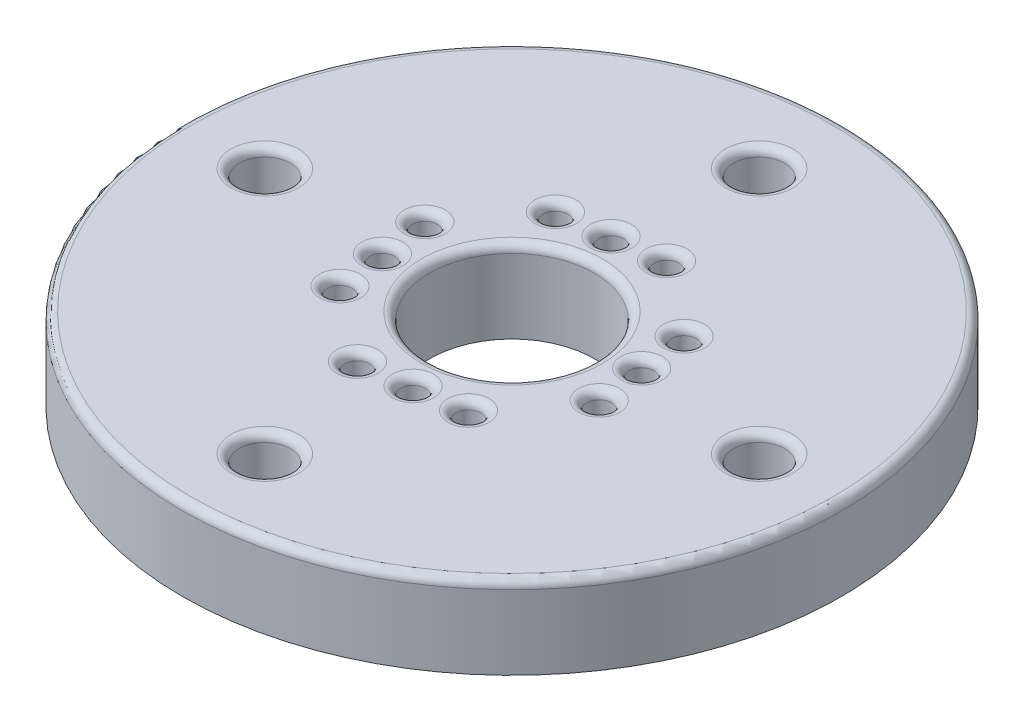
SolidWorks part; units mm, degrees
ref_plane "Piano frontale" through (0, 0, 0) normal (0, 0, 1) x (1, 0, 0)
ref_plane "Piano superiore" through (0, 0, 0) normal (0, 1, 0) x (1, 0, 0)
ref_plane "Piano destro" through (0, 0, 0) normal (1, 0, 0) x (0, 0, -1)
sketch "Schizzo1" plane through (0, 0, 0) normal (0, 1, 0) x (1, 0, 0)
  line L0 (0, 18.2203) -> (0, -20.6735) construction
  line L1 (-18.4196, 0) -> (19.4331, 0) construction
  circle A0 centre (0, 0) radius 15 construction
  circle A2 centre (0, 15) radius 1.55
  circle A3 centre (15, 0) radius 1.55
  circle A4 centre (0, -15) radius 1.55
  circle A5 centre (-15, 0) radius 1.55
  circle A6 centre (0, 0) radius 5
  circle A7 centre (0, 0) radius 20
  dimension "D1" = 30
  dimension "D2" = 3.1
  dimension "D3" = 10
  dimension "D4" = 40
extrude "Estrusione-Estrusione1" add sketch "Schizzo1" along normal blind 5
fillet "Raccordo1" radius 0.5 6 edges at (0, 5, 5) (0, 5, 16.55) (0, 5, -13.45) (0, 5, 20) (15, 5, 1.55) (-15, 5, 1.55)
sketch "Schizzo2" plane through (0, 0, 0) normal (0, -1, 0) x (1, 0, 0)
  circle A0 centre (0, 0) radius 10.35 construction
  circle A1 centre (0, 0) radius 20
  circle A2 centre (0, 0) radius 20
  circle A3 centre (-7.3362, -2.0447) radius 0.75 construction
  circle A4 centre (-6.9381, 0.9288) radius 0.75 construction
  circle A5 centre (-6.5401, 3.9023) radius 0.75 construction
  circle A6 centre (-2.0447, 7.3362) radius 0.75 construction
  circle A7 centre (0.9288, 6.9381) radius 0.75 construction
  circle A8 centre (3.9023, 6.5401) radius 0.75 construction
  circle A9 centre (7.3362, 2.0447) radius 0.75 construction
  circle A10 centre (6.9381, -0.9288) radius 0.75 construction
  circle A11 centre (6.5401, -3.9023) radius 0.75 construction
  circle A12 centre (2.0447, -7.3362) radius 0.75 construction
  circle A13 centre (-0.9288, -6.9381) radius 0.75 construction
  circle A14 centre (-3.9023, -6.5401) radius 0.75 construction
  circle A15 centre (0, 0) radius 10.35
  circle A16 centre (-7.3362, -2.0447) radius 0.75
  circle A17 centre (-6.9381, 0.9288) radius 0.75
  circle A18 centre (-6.5401, 3.9023) radius 0.75
  circle A19 centre (-2.0447, 7.3362) radius 0.75
  circle A20 centre (0.9288, 6.9381) radius 0.75
  circle A21 centre (3.9023, 6.5401) radius 0.75
  circle A22 centre (7.3362, 2.0447) radius 0.75
  circle A23 centre (6.9381, -0.9288) radius 0.75
  circle A24 centre (6.5401, -3.9023) radius 0.75
  circle A25 centre (2.0447, -7.3362) radius 0.75
  circle A26 centre (-0.9288, -6.9381) radius 0.75
  circle A27 centre (-3.9023, -6.5401) radius 0.75
  dimension "D1" = 0
extrude "Taglio-Estrusione4" cut sketch "Schizzo2" against normal through all both and the other way through all contours A17 | A16 | A27 | A18 | A26 | A25 | A24 | A23 | A22 | A21 | A20 | A19
fillet "Raccordo3" radius 0.5 12 edges at (-6.9381, 5, 0.1788) (-0.9288, 5, -7.6881) (-6.5401, 5, 3.1523) (-3.9023, 5, -7.2901) (-7.3362, 5, -2.7947) (2.0447, 5, -8.0862) (6.5401, 5, -4.6523) (6.9381, 5, -1.6788) (7.3362, 5, 1.2947) (3.9023, 5, 5.7901) (0.9288, 5, 6.1881) (-2.0447, 5, 6.5862)
